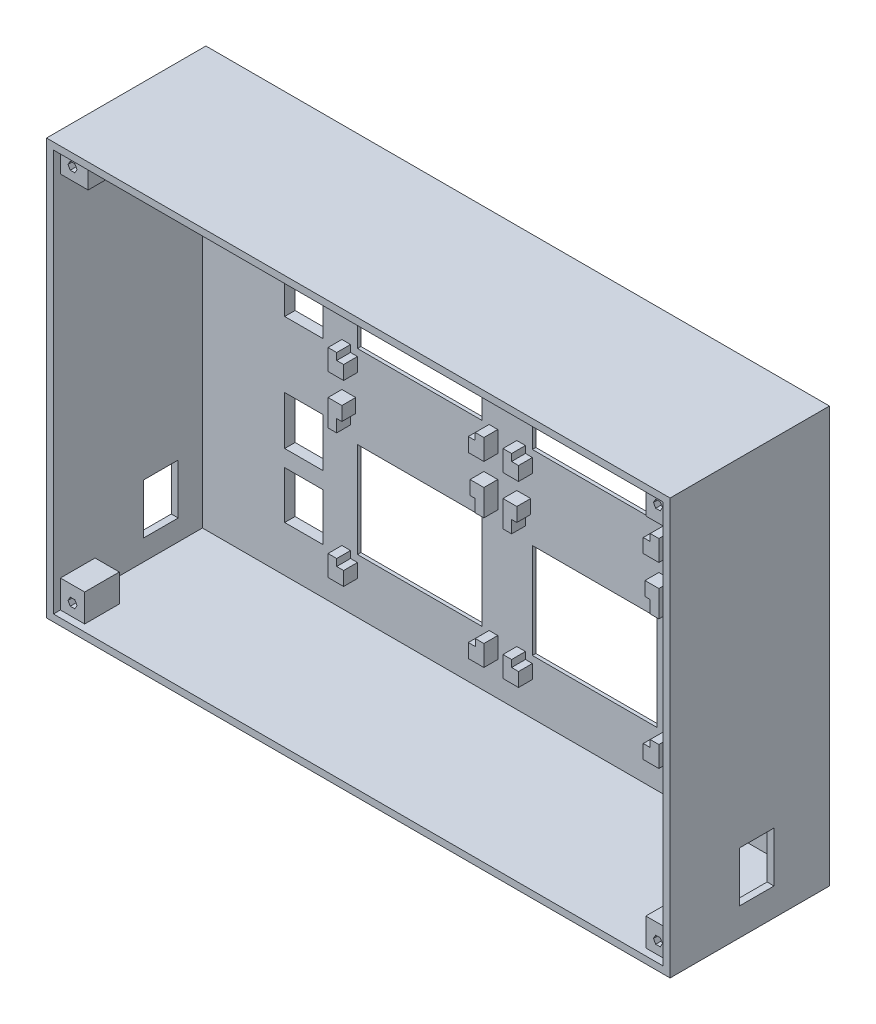
SolidWorks part; units mm, degrees
ref_plane "Front Plane" through (0, 0, 0) normal (0, 0, 1) x (1, 0, 0)
ref_plane "Top Plane" through (0, 0, 0) normal (0, 1, 0) x (1, 0, 0)
ref_plane "Right Plane" through (0, 0, 0) normal (1, 0, 0) x (0, 0, -1)
sketch "Sketch1" plane through (0, 0, 0) normal (0, 0, 1) x (1, 0, 0)
  line L1 (-78.1052, 76.2016) -> (101.8948, 76.2016)
  line L2 (-78.1052, 76.2016) -> (-78.1052, -43.7984)
  line L3 (-78.1052, -43.7984) -> (101.8948, -43.7984)
  line L4 (101.8948, 76.2016) -> (101.8948, -43.7984)
  dimension "D1" = 120
  dimension "D2" = 180
extrude "Boss-Extrude" add sketch "Sketch1" along normal blind 46
sketch "Sketch2" plane through (0, 0, 46) normal (0, 0, 1) x (1, 0, 0)
  line L0 (-78.1052, -43.7984) -> (101.8948, -43.7984) construction
  line L1 (-76.1052, 74.2016) -> (99.8948, 74.2016)
  line L2 (-76.1052, 74.2016) -> (-76.1052, -41.7984)
  line L3 (-76.1052, -41.7984) -> (99.8948, -41.7984)
  line L4 (99.8948, 74.2016) -> (99.8948, -41.7984)
  line L5 (-78.1052, 76.2016) -> (-78.1052, -43.7984) construction
  dimension "D1" = 116
  dimension "D2" = 176
  dimension "D3" = 2
  dimension "D4" = 2
extrude "Main Box" cut sketch "Sketch2" against normal blind 43
sketch "Sketch3" plane through (0, 0, 3) normal (0, 0, 1) x (1, 0, 0)
  line L0 (11.8948, 74.2016) -> (11.8948, -41.7984) construction
  line L1 (-76.1052, 16.2016) -> (99.8948, 16.2016) construction
  line L2 (19.1448, 52.9516) -> (19.1448, 25.4516)
  line L3 (-35.8552, 64.4516) -> (9.1448, 64.4516)
  line L4 (-35.8552, 64.4516) -> (-35.8552, 19.4516)
  line L5 (-35.8552, 19.4516) -> (9.1448, 19.4516)
  line L6 (9.1448, 64.4516) -> (9.1448, 19.4516)
  line L7 (-33.3552, 60.4516) -> (6.6448, 60.4516)
  line L8 (-33.3552, 60.4516) -> (-33.3552, 23.4516)
  line L9 (-33.3552, 23.4516) -> (6.6448, 23.4516)
  line L10 (6.6448, 60.4516) -> (6.6448, 23.4516)
  line L11 (-31.3552, 52.9516) -> (4.6448, 52.9516)
  line L12 (-31.3552, 52.9516) -> (-31.3552, 25.4516)
  line L13 (-31.3552, 25.4516) -> (4.6448, 25.4516)
  line L14 (4.6448, 52.9516) -> (4.6448, 25.4516)
  line L15 (55.1448, 25.4516) -> (19.1448, 25.4516)
  line L16 (55.1448, 52.9516) -> (55.1448, 25.4516)
  line L17 (55.1448, 52.9516) -> (19.1448, 52.9516)
  line L18 (17.1448, 60.4516) -> (17.1448, 23.4516)
  line L19 (57.1448, 23.4516) -> (17.1448, 23.4516)
  line L20 (57.1448, 60.4516) -> (57.1448, 23.4516)
  line L21 (57.1448, 60.4516) -> (17.1448, 60.4516)
  line L22 (14.6448, 64.4516) -> (14.6448, 19.4516)
  line L23 (59.6448, 19.4516) -> (14.6448, 19.4516)
  line L24 (59.6448, 64.4516) -> (59.6448, 19.4516)
  line L25 (59.6448, 64.4516) -> (14.6448, 64.4516)
  line L26 (-31.3552, 1.4516) -> (-31.3552, -26.0484)
  line L27 (14.6448, 12.9516) -> (59.6448, 12.9516)
  line L28 (14.6448, 12.9516) -> (14.6448, -32.0484)
  line L29 (14.6448, -32.0484) -> (59.6448, -32.0484)
  line L30 (59.6448, 12.9516) -> (59.6448, -32.0484)
  line L31 (17.1448, 8.9516) -> (57.1448, 8.9516)
  line L32 (17.1448, 8.9516) -> (17.1448, -28.0484)
  line L33 (17.1448, -28.0484) -> (57.1448, -28.0484)
  line L34 (57.1448, 8.9516) -> (57.1448, -28.0484)
  line L35 (19.1448, 1.4516) -> (55.1448, 1.4516)
  line L36 (19.1448, 1.4516) -> (19.1448, -26.0484)
  line L37 (19.1448, -26.0484) -> (55.1448, -26.0484)
  line L38 (55.1448, 1.4516) -> (55.1448, -26.0484)
  line L39 (4.6448, -26.0484) -> (-31.3552, -26.0484)
  line L40 (4.6448, 1.4516) -> (4.6448, -26.0484)
  line L41 (4.6448, 1.4516) -> (-31.3552, 1.4516)
  line L42 (-33.3552, 8.9516) -> (-33.3552, -28.0484)
  line L43 (6.6448, -28.0484) -> (-33.3552, -28.0484)
  line L44 (6.6448, 8.9516) -> (6.6448, -28.0484)
  line L45 (6.6448, 8.9516) -> (-33.3552, 8.9516)
  line L46 (-35.8552, 12.9516) -> (-35.8552, -32.0484)
  line L47 (9.1448, -32.0484) -> (-35.8552, -32.0484)
  line L48 (9.1448, 12.9516) -> (9.1448, -32.0484)
  line L49 (9.1448, 12.9516) -> (-35.8552, 12.9516)
  dimension "D1" = 45
  dimension "D2" = 45
  dimension "D3" = 2.75
  dimension "D4" = 3.25
  dimension "D5" = 37
  dimension "D6" = 40
  dimension "D7" = 4
  dimension "D8" = 2.5
  dimension "D9" = 2
  dimension "D10" = 36
  dimension "D11" = 2
  dimension "D12" = 27.5
  dimension "D13" = 45
  dimension "D14" = 45
  dimension "D15" = 40
  dimension "D16" = 3.25
  dimension "D17" = 2.75
  dimension "D18" = 2.5
  dimension "D19" = 2
  dimension "D20" = 36
  dimension "D21" = 27.5
  dimension "D22" = 37
  dimension "D23" = 2
  dimension "D24" = 4
extrude "Display" cut sketch "Sketch3" against normal through all contours L16 L17 L2 L15 | L40 L41 L26 L39 | L38 L35 L36 L37 | L12 L11 L14 L13
sketch "Sketch36" plane through (0, 0, 3) normal (0, 0, 1) x (1, 0, 0)
  line L0 (-35.8552, 12.9516) -> (9.1448, 12.9516) construction
  line L1 (-35.8552, 12.9516) -> (-31.8552, 12.9516)
  line L2 (-35.8552, 12.9516) -> (-35.8552, 5.3516)
  line L3 (-35.8552, 5.3516) -> (-31.8552, 5.3516)
  line L4 (-31.8552, 12.9516) -> (-31.8552, 5.3516)
  line L5 (-13.3552, 12.9516) -> (-13.3552, -31.753) construction
  line L6 (9.1448, 5.3516) -> (5.1448, 5.3516)
  line L7 (5.1448, 12.9516) -> (5.1448, 5.3516)
  line L8 (9.1448, 12.9516) -> (5.1448, 12.9516)
  line L9 (9.1448, 12.9516) -> (9.1448, 5.3516)
  line L10 (11.8948, 74.2016) -> (11.8948, -41.7984) construction
  line L11 (14.6448, 12.9516) -> (14.6448, 5.3516)
  line L12 (14.6448, 12.9516) -> (18.6448, 12.9516)
  line L13 (18.6448, 12.9516) -> (18.6448, 5.3516)
  line L14 (14.6448, 5.3516) -> (18.6448, 5.3516)
  line L15 (59.6448, 5.3516) -> (55.6448, 5.3516)
  line L16 (55.6448, 12.9516) -> (55.6448, 5.3516)
  line L17 (59.6448, 12.9516) -> (55.6448, 12.9516)
  line L18 (59.6448, 12.9516) -> (59.6448, 5.3516)
  dimension "D1" = 7.6
  dimension "D2" = 4
extrude "Boss-Extrude8" add sketch "Sketch36" along normal blind 4
sketch "Sketch39" plane through (0, 0, 7) normal (0, 0, 1) x (1, 0, 0)
  line L0 (9.1448, 12.9516) -> (5.1448, 12.9516) construction
  line L1 (5.1448, 5.3516) -> (6.6448, 5.3516)
  line L2 (5.1448, 5.3516) -> (5.1448, 8.9516)
  line L3 (5.1448, 8.9516) -> (6.6448, 8.9516)
  line L4 (6.6448, 5.3516) -> (6.6448, 8.9516)
  line L5 (9.1448, 5.3516) -> (9.1448, 12.9516) construction
  dimension "D1" = 4
  dimension "D2" = 2.5
extrude "Cut-Extrude25" cut sketch "Sketch39" against normal blind 4
sketch "Sketch38" plane through (0, 0, 7) normal (0, 0, 1) x (1, 0, 0)
  line L0 (-31.8552, 12.9516) -> (-35.8552, 12.9516) construction
  line L1 (-31.8552, 5.3516) -> (-33.3552, 5.3516)
  line L2 (-31.8552, 5.3516) -> (-31.8552, 8.9516)
  line L3 (-31.8552, 8.9516) -> (-33.3552, 8.9516)
  line L4 (-33.3552, 5.3516) -> (-33.3552, 8.9516)
  line L5 (-35.8552, 12.9516) -> (-35.8552, 5.3516) construction
  point P5 (-32.6052, 8.9516)
  point P8 (-33.3552, 7.1516)
  dimension "D1" = 4
  dimension "D2" = 2.5
extrude "Cut-Extrude24" cut sketch "Sketch38" against normal blind 4
sketch "Sketch40" plane through (0, 0, 7) normal (0, 0, 1) x (1, 0, 0)
  line L0 (14.6448, 12.9516) -> (14.6448, 5.3516) construction
  line L1 (18.6448, 5.3516) -> (17.1448, 5.3516)
  line L2 (18.6448, 5.3516) -> (18.6448, 8.9516)
  line L3 (18.6448, 8.9516) -> (17.1448, 8.9516)
  line L4 (17.1448, 5.3516) -> (17.1448, 8.9516)
  line L5 (14.6448, 12.9516) -> (59.6448, 12.9516) construction
  dimension "D1" = 2.5
  dimension "D2" = 4
extrude "Cut-Extrude26" cut sketch "Sketch40" against normal blind 4
sketch "Sketch29" plane through (0, 0, 3) normal (0, 0, 1) x (1, 0, 0)
  line L0 (-35.8552, 19.4516) -> (9.1448, 64.4516) construction
  line L1 (-35.8552, 64.4516) -> (-31.8552, 64.4516)
  line L2 (-35.8552, 64.4516) -> (-35.8552, 56.8516)
  line L3 (-35.8552, 56.8516) -> (-31.8552, 56.8516)
  line L4 (-31.8552, 64.4516) -> (-31.8552, 56.8516)
  line L5 (-13.3552, 64.2016) -> (-13.3552, 19.2016) construction
  line L7 (9.1448, 56.8516) -> (5.1448, 56.8516)
  line L8 (5.1448, 64.4516) -> (5.1448, 56.8516)
  line L9 (9.1448, 64.4516) -> (5.1448, 64.4516)
  line L10 (9.1448, 64.4516) -> (9.1448, 56.8516)
  line L11 (11.8948, 74.2016) -> (11.8948, -41.7984) construction
  line L12 (14.6448, 64.4516) -> (14.6448, 56.8516)
  line L13 (14.6448, 64.4516) -> (18.6448, 64.4516)
  line L14 (18.6448, 64.4516) -> (18.6448, 56.8516)
  line L15 (14.6448, 56.8516) -> (18.6448, 56.8516)
  line L16 (59.6448, 56.8516) -> (55.6448, 56.8516)
  line L17 (55.6448, 64.4516) -> (55.6448, 56.8516)
  line L18 (59.6448, 64.4516) -> (55.6448, 64.4516)
  line L19 (59.6448, 64.4516) -> (59.6448, 56.8516)
  dimension "D1" = 4
  dimension "D2" = 7.6
extrude "Boss-Extrude4" add sketch "Sketch29" along normal blind 4 contours L12 L15 L14 L13 | L19 L18 L17 L16 | L2 L1 L4 L3 | L10 L7 L8 L9
sketch "Sketch31" plane through (0, 0, 7) normal (0, 0, 1) x (1, 0, 0)
  line L0 (-35.8552, 64.4516) -> (-31.8552, 64.4516) construction
  line L1 (-31.8552, 56.8516) -> (-33.3552, 56.8516)
  line L2 (-31.8552, 56.8516) -> (-31.8552, 60.4516)
  line L3 (-31.8552, 60.4516) -> (-33.3552, 60.4516)
  line L4 (-33.3552, 56.8516) -> (-33.3552, 60.4516)
  line L5 (-35.8552, 64.4516) -> (-35.8552, 56.8516) construction
  line L6 (9.1448, 64.4516) -> (9.1448, 56.8516) construction
  line L7 (5.1448, 56.8516) -> (6.6448, 56.8516)
  line L8 (5.1448, 56.8516) -> (5.1448, 60.4516)
  line L9 (5.1448, 60.4516) -> (6.6448, 60.4516)
  line L10 (6.6448, 56.8516) -> (6.6448, 60.4516)
  line L11 (9.1448, 64.4516) -> (5.1448, 64.4516) construction
  line L12 (14.6448, 64.4516) -> (14.6448, 56.8516) construction
  line L13 (18.6448, 56.8516) -> (17.1448, 56.8516)
  line L14 (18.6448, 56.8516) -> (18.6448, 60.4516)
  line L15 (18.6448, 60.4516) -> (17.1448, 60.4516)
  line L16 (17.1448, 56.8516) -> (17.1448, 60.4516)
  line L17 (14.6448, 64.4516) -> (18.6448, 64.4516) construction
  line L18 (59.6448, 64.4516) -> (59.6448, 56.8516) construction
  line L19 (55.6448, 56.8516) -> (57.1448, 56.8516)
  line L20 (55.6448, 56.8516) -> (55.6448, 60.4516)
  line L21 (55.6448, 60.4516) -> (57.1448, 60.4516)
  line L22 (57.1448, 56.8516) -> (57.1448, 60.4516)
  line L23 (59.6448, 64.4516) -> (55.6448, 64.4516) construction
  dimension "D1" = 4
  dimension "D2" = 2.5
  dimension "D3" = 2.5
  dimension "D4" = 4
  dimension "D5" = 2.5
  dimension "D6" = 4
  dimension "D7" = 2.5
  dimension "D8" = 4
extrude "Cut-Extrude21" cut sketch "Sketch31" against normal blind 4
sketch "Sketch32" plane through (0, 0, 3) normal (0, 0, 1) x (1, 0, 0)
  line L1 (-35.8552, 19.4516) -> (-31.3552, 19.4516)
  line L2 (-35.8552, 19.4516) -> (-35.8552, 25.4516)
  line L3 (-35.8552, 25.4516) -> (-31.3552, 25.4516)
  line L4 (-31.3552, 19.4516) -> (-31.3552, 25.4516)
  line L5 (9.1448, 19.4516) -> (4.6448, 19.4516)
  line L6 (9.1448, 19.4516) -> (9.1448, 25.4516)
  line L7 (9.1448, 25.4516) -> (4.6448, 25.4516)
  line L8 (4.6448, 19.4516) -> (4.6448, 25.4516)
  line L9 (14.6448, 19.4516) -> (19.1448, 19.4516)
  line L10 (14.6448, 19.4516) -> (14.6448, 25.4516)
  line L11 (14.6448, 25.4516) -> (19.1448, 25.4516)
  line L12 (19.1448, 19.4516) -> (19.1448, 25.4516)
  line L13 (59.6448, 19.4516) -> (55.1448, 19.4516)
  line L14 (59.6448, 19.4516) -> (59.6448, 25.4516)
  line L15 (59.6448, 25.4516) -> (55.1448, 25.4516)
  line L16 (55.1448, 19.4516) -> (55.1448, 25.4516)
extrude "Boss-Extrude5" add sketch "Sketch32" along normal blind 4
sketch "Sketch33" plane through (0, 0, 7) normal (0, 0, 1) x (1, 0, 0)
  line L0 (-35.8552, 25.4516) -> (-35.8552, 19.4516) construction
  line L1 (-31.3552, 25.4516) -> (-33.3552, 25.4516)
  line L2 (-31.3552, 25.4516) -> (-31.3552, 23.4516)
  line L3 (-31.3552, 23.4516) -> (-33.3552, 23.4516)
  line L4 (-33.3552, 25.4516) -> (-33.3552, 23.4516)
  line L5 (-35.8552, 19.4516) -> (9.1448, 19.4516) construction
  line L7 (4.6448, 25.4516) -> (6.6448, 25.4516)
  line L8 (4.6448, 25.4516) -> (4.6448, 23.4516)
  line L9 (4.6448, 23.4516) -> (6.6448, 23.4516)
  line L10 (6.6448, 25.4516) -> (6.6448, 23.4516)
  line L14 (9.1448, 19.4516) -> (9.1448, 25.4516) construction
  line L16 (14.6448, 19.4516) -> (19.1448, 19.4516) construction
  line L17 (19.1448, 25.4516) -> (17.1448, 25.4516)
  line L18 (19.1448, 25.4516) -> (19.1448, 23.4516)
  line L19 (19.1448, 23.4516) -> (17.1448, 23.4516)
  line L20 (17.1448, 25.4516) -> (17.1448, 23.4516)
  line L21 (14.6448, 25.4516) -> (14.6448, 19.4516) construction
  line L22 (59.6448, 19.4516) -> (59.6448, 25.4516) construction
  line L23 (55.1448, 25.4516) -> (57.1448, 25.4516)
  line L24 (55.1448, 25.4516) -> (55.1448, 23.4516)
  line L25 (55.1448, 23.4516) -> (57.1448, 23.4516)
  line L26 (57.1448, 25.4516) -> (57.1448, 23.4516)
  line L27 (55.1448, 19.4516) -> (59.6448, 19.4516) construction
  point P14 (5.6448, 25.4516)
  dimension "D1" = 2.5
  dimension "D2" = 4
  dimension "D3" = 2.5
  dimension "D4" = 2
  dimension "D5" = 4
  dimension "D6" = 2.5
  dimension "D7" = 2.5
  dimension "D8" = 4
extrude "Cut-Extrude22" cut sketch "Sketch33" against normal blind 4
sketch "Sketch34" plane through (0, 0, 3) normal (0, 0, 1) x (1, 0, 0)
  line L1 (-35.8552, -32.0484) -> (-31.3552, -32.0484)
  line L2 (-35.8552, -32.0484) -> (-35.8552, -26.0484)
  line L3 (-35.8552, -26.0484) -> (-31.3552, -26.0484)
  line L4 (-31.3552, -32.0484) -> (-31.3552, -26.0484)
  line L5 (9.1448, -32.0484) -> (4.6448, -32.0484)
  line L6 (9.1448, -32.0484) -> (9.1448, -26.0484)
  line L7 (9.1448, -26.0484) -> (4.6448, -26.0484)
  line L8 (4.6448, -32.0484) -> (4.6448, -26.0484)
  line L10 (14.6448, -32.0484) -> (19.1448, -32.0484)
  line L11 (14.6448, -32.0484) -> (14.6448, -26.0484)
  line L12 (14.6448, -26.0484) -> (19.1448, -26.0484)
  line L13 (19.1448, -32.0484) -> (19.1448, -26.0484)
  line L14 (59.6448, -32.0484) -> (55.1448, -32.0484)
  line L15 (59.6448, -32.0484) -> (59.6448, -26.0484)
  line L16 (59.6448, -26.0484) -> (55.1448, -26.0484)
  line L17 (55.1448, -32.0484) -> (55.1448, -26.0484)
extrude "Boss-Extrude7" add sketch "Sketch34" along normal blind 4
sketch "Sketch35" plane through (0, 0, 7) normal (0, 0, 1) x (1, 0, 0)
  line L1 (-31.3552, -26.0484) -> (-33.3552, -26.0484)
  line L2 (-31.3552, -26.0484) -> (-31.3552, -28.0484)
  line L3 (-31.3552, -28.0484) -> (-33.3552, -28.0484)
  line L4 (-33.3552, -26.0484) -> (-33.3552, -28.0484)
  line L5 (-35.8552, -32.0484) -> (-31.3552, -32.0484) construction
  line L6 (-35.8552, -26.0484) -> (-35.8552, -32.0484) construction
  line L7 (4.6448, -32.0484) -> (9.1448, -32.0484) construction
  line L8 (4.6448, -26.0484) -> (6.648, -26.0484)
  line L9 (4.6448, -26.0484) -> (4.6448, -28.0484)
  line L10 (4.6448, -28.0484) -> (6.648, -28.0484)
  line L11 (6.648, -26.0484) -> (6.648, -28.0484)
  line L12 (9.1448, 12.9516) -> (9.1448, -32.0484) construction
  line L13 (14.6448, -26.0484) -> (14.6448, -32.0484) construction
  line L14 (19.1448, -26.0484) -> (17.1448, -26.0484)
  line L15 (19.1448, -26.0484) -> (19.1448, -28.0484)
  line L16 (19.1448, -28.0484) -> (17.1448, -28.0484)
  line L17 (17.1448, -26.0484) -> (17.1448, -28.0484)
  line L18 (14.6448, -32.0484) -> (19.1448, -32.0484) construction
  line L19 (59.6448, -32.0484) -> (59.6448, -26.0484) construction
  line L20 (55.1448, -26.0484) -> (57.1448, -26.0484)
  line L21 (55.1448, -26.0484) -> (55.1448, -28.0484)
  line L22 (55.1448, -28.0484) -> (57.1448, -28.0484)
  line L23 (57.1448, -26.0484) -> (57.1448, -28.0484)
  line L24 (55.1448, -32.0484) -> (59.6448, -32.0484) construction
  dimension "D1" = 4
  dimension "D2" = 2.5
  dimension "D3" = 4
  dimension "D4" = 2.4967
  dimension "D5" = 2.5
  dimension "D6" = 4
  dimension "D7" = 2.5
  dimension "D8" = 4
extrude "Cut-Extrude23" cut sketch "Sketch35" against normal blind 4
sketch "Sketch43" plane through (0, 0, 7) normal (0, 0, 1) x (1, 0, 0)
  line L0 (59.6448, 12.9516) -> (55.6448, 12.9516) construction
  line L1 (55.6448, 5.3516) -> (57.1448, 5.3516)
  line L2 (55.6448, 5.3516) -> (55.6448, 8.9516)
  line L3 (55.6448, 8.9516) -> (57.1448, 8.9516)
  line L4 (57.1448, 5.3516) -> (57.1448, 8.9516)
  line L5 (59.6448, 5.3516) -> (59.6448, 12.9516) construction
  dimension "D1" = 4
  dimension "D2" = 2.5
extrude "Cut-Extrude28" cut sketch "Sketch43" against normal blind 4
sketch "Sketch7" plane through (0, 0, 3) normal (0, 0, 1) x (1, 0, 0)
  line L0 (11.8948, 74.2016) -> (11.8948, -41.7984) construction
  line L1 (-52.3552, 36.9516) -> (-41.3552, 36.9516)
  line L2 (-52.3552, 36.9516) -> (-52.3552, 22.9516)
  line L3 (-52.3552, 22.9516) -> (-41.3552, 22.9516)
  line L4 (-41.3552, 36.9516) -> (-41.3552, 22.9516)
  line L5 (-76.1052, 16.2016) -> (99.8948, 16.2016) construction
  line L6 (4.6448, 1.4516) -> (-31.3552, 1.4516) construction
  line L7 (-31.3552, 52.9516) -> (-31.3552, 25.4516) construction
  line L8 (-52.3552, 55.4516) -> (-41.3552, 55.4516)
  line L9 (-52.3552, 55.4516) -> (-52.3552, 41.4516)
  line L10 (-52.3552, 41.4516) -> (-41.3552, 41.4516)
  line L11 (-41.3552, 55.4516) -> (-41.3552, 41.4516)
  line L12 (-52.3552, 3.9516) -> (-41.3552, 3.9516)
  line L13 (-31.3552, 52.9516) -> (4.6448, 52.9516) construction
  line L14 (-31.3552, 25.4516) -> (4.6448, 25.4516) construction
  line L15 (65.1448, 55.4516) -> (65.1448, 41.4516)
  line L16 (76.1448, 41.4516) -> (65.1448, 41.4516)
  line L17 (76.1448, 55.4516) -> (76.1448, 41.4516)
  line L18 (76.1448, 55.4516) -> (65.1448, 55.4516)
  line L19 (65.1448, 36.9516) -> (65.1448, 22.9516)
  line L20 (76.1448, 22.9516) -> (65.1448, 22.9516)
  line L21 (76.1448, 36.9516) -> (76.1448, 22.9516)
  line L22 (76.1448, 36.9516) -> (65.1448, 36.9516)
  line L23 (-52.3552, 3.9516) -> (-52.3552, -10.0484)
  line L24 (-52.3552, -10.0484) -> (-41.3552, -10.0484)
  line L25 (-41.3552, 3.9516) -> (-41.3552, -10.0484)
  line L26 (-31.3552, 1.4516) -> (-31.3552, -26.0484) construction
  line L27 (-52.3552, -14.8273) -> (-41.3552, -14.8273)
  line L28 (-52.3552, -14.8273) -> (-52.3552, -28.5484)
  line L29 (-52.3552, -28.5484) -> (-41.3552, -28.5484)
  line L30 (-41.3552, -14.8273) -> (-41.3552, -28.5484)
  line L31 (4.6448, -26.0484) -> (-31.3552, -26.0484) construction
  line L32 (65.1448, -14.8273) -> (65.1448, -28.5484)
  line L33 (76.1448, -28.5484) -> (65.1448, -28.5484)
  line L34 (76.1448, -14.8273) -> (76.1448, -28.5484)
  line L35 (76.1448, -14.8273) -> (65.1448, -14.8273)
  line L36 (65.1448, 3.9516) -> (65.1448, -10.0484)
  line L37 (76.1448, -10.0484) -> (65.1448, -10.0484)
  line L38 (76.1448, 3.9516) -> (76.1448, -10.0484)
  line L39 (76.1448, 3.9516) -> (65.1448, 3.9516)
  dimension "D1" = 14
  dimension "D2" = 11
  dimension "D3" = 2.5
  dimension "D4" = 10
  dimension "D5" = 11
  dimension "D6" = 14
  dimension "D7" = 10
  dimension "D8" = 2.5
  dimension "D9" = 14
  dimension "D10" = 2.5
  dimension "D11" = 10
  dimension "D12" = 11
  dimension "D13" = 10
  dimension "D14" = 11
  dimension "D15" = 2.5
  dimension "D16" = 4.7788
extrude "Push Button" cut sketch "Sketch7" against normal through all contours L4 L1 L2 L3 | L17 L18 L15 L16 | L21 L22 L19 L20 | L38 L39 L36 L37 | L34 L35 L32 L33 | L30 L27 L28 L29 | L25 L12 L23 L24 | L8 L11 L10 L9
sketch "Sketch27" plane through (101.8948, 0, 0) normal (1, 0, 0) x (0, 0, -1)
  line L0 (-46, -43.7984) -> (-46, 76.2016) construction
  line L1 (-26, -21.2984) -> (-16, -21.2984)
  line L2 (-26, -21.2984) -> (-26, -35.7984)
  line L3 (-26, -35.7984) -> (-16, -35.7984)
  line L4 (-16, -21.2984) -> (-16, -35.7984)
  line L7 (-46, -43.7984) -> (0, -43.7984) construction
  dimension "D1" = 14.5
  dimension "D2" = 10
  dimension "D3" = 20
  dimension "D4" = 8
extrude "Cut-Extrude17" cut sketch "Sketch27" against normal blind 3
sketch "Sketch28" plane through (-78.1052, 0, 0) normal (-1, 0, 0) x (0, 0, 1)
  line L0 (46, -43.7984) -> (0, -43.7984) construction
  line L1 (10, -21.2984) -> (20, -21.2984)
  line L2 (10, -21.2984) -> (10, -35.7984)
  line L3 (10, -35.7984) -> (20, -35.7984)
  line L4 (20, -21.2984) -> (20, -35.7984)
  line L5 (0, 76.2016) -> (0, -43.7984) construction
  dimension "D1" = 14.5
  dimension "D2" = 10
  dimension "D3" = 8
  dimension "D4" = 10
extrude "Cut-Extrude18" cut sketch "Sketch28" against normal blind 3
sketch "Sketch45" plane through (0, 74.2016, 0) normal (0, -1, 0) x (1, 0, 0)
  line L0 (-76.1052, 3) -> (-76.1052, 46) construction
  line L1 (-76.1052, 44) -> (-68.1052, 44)
  line L2 (-76.1052, 44) -> (-76.1052, 28)
  line L3 (-76.1052, 28) -> (-68.1052, 28)
  line L4 (-68.1052, 44) -> (-68.1052, 28)
  line L5 (99.8948, 46) -> (-76.1052, 46) construction
  dimension "D1" = 2
  dimension "D2" = 16
  dimension "D3" = 8
extrude "Boss-Extrude10" add sketch "Sketch45" along normal blind 7
sketch "Sketch46" plane through (99.8948, 0, 0) normal (-1, 0, 0) x (0, 0, 1)
  line L0 (3, 74.2016) -> (46, 74.2016) construction
  line L1 (44, 74.2016) -> (28, 74.2016)
  line L2 (44, 74.2016) -> (44, 66.2016)
  line L3 (44, 66.2016) -> (28, 66.2016)
  line L4 (28, 74.2016) -> (28, 66.2016)
  line L5 (46, -41.7984) -> (46, 74.2016) construction
  dimension "D1" = 2
  dimension "D2" = 16
  dimension "D3" = 8
extrude "Boss-Extrude11" add sketch "Sketch46" along normal blind 7
sketch "Sketch47" plane through (99.8948, 0, 0) normal (-1, 0, 0) x (0, 0, 1)
  line L0 (3, -41.7984) -> (46, -41.7984) construction
  line L1 (28, -41.7984) -> (44, -41.7984)
  line L2 (28, -41.7984) -> (28, -33.7984)
  line L3 (28, -33.7984) -> (44, -33.7984)
  line L4 (44, -41.7984) -> (44, -33.7984)
  line L5 (46, -41.7984) -> (46, 74.2016) construction
  dimension "D1" = 2
  dimension "D2" = 8
  dimension "D3" = 16
extrude "Boss-Extrude12" add sketch "Sketch47" along normal blind 7
sketch "Sketch48" plane through (-76.1052, 0, 0) normal (1, 0, 0) x (0, 0, -1)
  line L0 (-3, -41.7984) -> (-46, -41.7984) construction
  line L1 (-44, -41.7984) -> (-28, -41.7984)
  line L2 (-44, -41.7984) -> (-44, -33.7984)
  line L3 (-44, -33.7984) -> (-28, -33.7984)
  line L4 (-28, -41.7984) -> (-28, -33.7984)
  line L5 (-46, 74.2016) -> (-46, -41.7984) construction
  dimension "D1" = 2
  dimension "D2" = 8
  dimension "D3" = 16
extrude "Boss-Extrude13" add sketch "Sketch48" along normal blind 7
sketch "Sketch49" plane through (0, 0, 44) normal (0, 0, 1) x (1, 0, 0)
  line L0 (99.8948, 74.2016) -> (-76.1052, 74.2016) construction
  line L1 (-73.2599, 71.8355) -> (-73.9146, 70.7016)
  line L2 (-73.9146, 70.7016) -> (-73.2599, 69.5676)
  line L3 (-73.2599, 69.5676) -> (-71.9505, 69.5676)
  line L4 (-71.9505, 69.5676) -> (-71.2958, 70.7016)
  line L5 (-71.2958, 70.7016) -> (-71.9505, 71.8355)
  line L6 (-71.9505, 71.8355) -> (-73.2599, 71.8355)
  line L7 (-76.1052, 74.2016) -> (-76.1052, -41.7984) construction
  line L8 (11.8948, 74.2016) -> (11.8948, -41.7984) construction
  line L9 (-76.1052, -41.7984) -> (99.8948, -41.7984) construction
  line L10 (-76.1052, 16.2016) -> (99.8948, 16.2016) construction
  line L11 (99.8948, -41.7984) -> (99.8948, 74.2016) construction
  line L12 (-71.9505, -39.4324) -> (-73.2599, -39.4324)
  line L13 (-71.2958, -38.2984) -> (-71.9505, -39.4324)
  line L14 (-71.9505, -37.1645) -> (-71.2958, -38.2984)
  line L15 (-73.2599, -37.1645) -> (-71.9505, -37.1645)
  line L16 (-73.9146, -38.2984) -> (-73.2599, -37.1645)
  line L17 (-73.2599, -39.4324) -> (-73.9146, -38.2984)
  line L18 (97.0495, -39.4324) -> (97.7042, -38.2984)
  line L19 (97.7042, -38.2984) -> (97.0495, -37.1645)
  line L20 (97.0495, -37.1645) -> (95.7401, -37.1645)
  line L21 (95.7401, -37.1645) -> (95.0854, -38.2984)
  line L22 (95.0854, -38.2984) -> (95.7401, -39.4324)
  line L23 (95.7401, -39.4324) -> (97.0495, -39.4324)
  line L24 (95.7401, 69.5676) -> (95.0854, 70.7016)
  line L25 (95.0854, 70.7016) -> (95.7401, 71.8355)
  line L26 (95.7401, 71.8355) -> (97.0495, 71.8355)
  line L27 (97.0495, 69.5676) -> (95.7401, 69.5676)
  line L28 (97.7042, 70.7016) -> (97.0495, 69.5676)
  line L29 (97.0495, 71.8355) -> (97.7042, 70.7016)
  circle A0 centre (-72.6052, 70.7016) radius 1.134 construction
  circle A1 centre (-72.6052, -38.2984) radius 1.134 construction
  circle A2 centre (96.3948, -38.2984) radius 1.134 construction
  circle A3 centre (96.3948, 70.7016) radius 1.134 construction
  dimension "D1" = 3.5
  dimension "D2" = 3.5
extrude "Cut-Extrude29" cut sketch "Sketch49" against normal blind 10
sketch "Sketch50" plane through (-78.1052, 0, 0) normal (-1, 0, 0) x (0, 0, 1)
  circle A0 centre (23.2353, 59.2153) radius 4
extrude "Cut-Extrude30" cut sketch "Sketch50" against normal blind 10
chamfer "Chamfer1" distance 6 angle 45 8 edges at (-72.6052, -33.7984, 28) (-69.1052, -37.7984, 28) (92.8948, 70.2016, 28) (96.3948, 66.2016, 28) (-68.1052, 70.7016, 28) (-72.1052, 67.2016, 28) (96.3948, -33.7984, 28) (92.8948, -37.7984, 28)
chamfer "Chamfer2" distance 2 angle 45 17 edges at (-31.3552, 39.2016, 0) (-13.3552, 25.4516, 0) (4.6448, 39.2016, 0) (-13.3552, 52.9516, 0) (37.1448, 25.4516, 0) (55.1448, 39.2016, 0) (37.1448, 52.9516, 0) (19.1448, 39.2016, 0) (19.1448, -12.2984, 0) (37.1448, -26.0484, 0) (55.1448, -12.2984, 0) (37.1448, 1.4516, 0) (-13.3552, 1.4516, 0) (4.6448, -12.2984, 0) (-13.3552, -26.0484, 0) (-31.3552, -12.2984, 0) (99.8948, -41.7984, 15.5)
sketch "Sketch44" plane through (0, 0, 3) normal (0, 0, 1) x (1, 0, 0)
  line L0 (-34.8352, 64.2016) -> (-30.8352, 64.2016) construction
  line L1 (-37.1707, 66.2201) -> (58.4203, 66.2201)
  line L2 (-37.1707, 66.2201) -> (-37.1707, -33.8169)
  line L3 (-37.1707, -33.8169) -> (58.4203, -33.8169)
  line L4 (58.4203, 66.2201) -> (58.4203, -33.8169)
  line L5 (58.6248, 64.2016) -> (58.6248, 56.6016) construction
  line L7 (-22.9402, 64.2231) -> (-1.7302, 64.2231)
  line L8 (-22.9402, 64.2231) -> (-22.9402, 60.0321)
  line L9 (-22.9402, 60.0321) -> (-1.7302, 60.0321)
  line L10 (-1.7302, 64.2231) -> (-1.7302, 60.0321)
  line L14 (25.5198, 64.2231) -> (46.7298, 64.2231)
  line L19 (25.5198, 64.2231) -> (25.5198, 60.0321)
  line L20 (25.5198, 60.0321) -> (46.7298, 60.0321)
  line L21 (46.7298, 64.2231) -> (46.7298, 60.0321)
  line L22 (25.5198, 12.1531) -> (46.7298, 12.1531)
  line L27 (25.5198, 12.1531) -> (25.5198, 7.9621)
  line L28 (25.5198, 7.9621) -> (46.7298, 7.9621)
  line L29 (46.7298, 12.1531) -> (46.7298, 7.9621)
  line L30 (-22.9402, 12.1531) -> (-1.7302, 12.1531)
  line L31 (-22.9402, 12.1531) -> (-22.9402, 7.9621)
  line L32 (-22.9402, 7.9621) -> (-1.7302, 7.9621)
  line L33 (-1.7302, 12.1531) -> (-1.7302, 7.9621)
  line L38 (-32.3352, 60.2016) -> (-32.3352, 23.2016) construction
  line L41 (16.1248, 60.2016) -> (16.1248, 23.2016) construction
  line L42 (-32.3352, 9.2016) -> (-32.3352, -27.7984) construction
  line L43 (16.1248, 9.2016) -> (16.1248, -27.7984) construction
  dimension "D1" = 95.591
  dimension "D2" = 100.037
  dimension "D3" = 2.0185
  dimension "D4" = 0.2045
  dimension "D5" = 21.21
  dimension "D6" = 4.191
  dimension "D7" = 1.997
  dimension "D8" = 1.997
  dimension "D9" = 47.879
  dimension "D10" = 9.395
  dimension "D11" = 9.395
  dimension "D12" = 9.395
  dimension "D13" = 21.21
  dimension "D14" = 21.21
  dimension "D15" = 4.191
  dimension "D16" = 21.21
  dimension "D17" = 4.191
  dimension "D18" = 4.191
  dimension "D19" = 47.879
  dimension "D20" = 9.395
